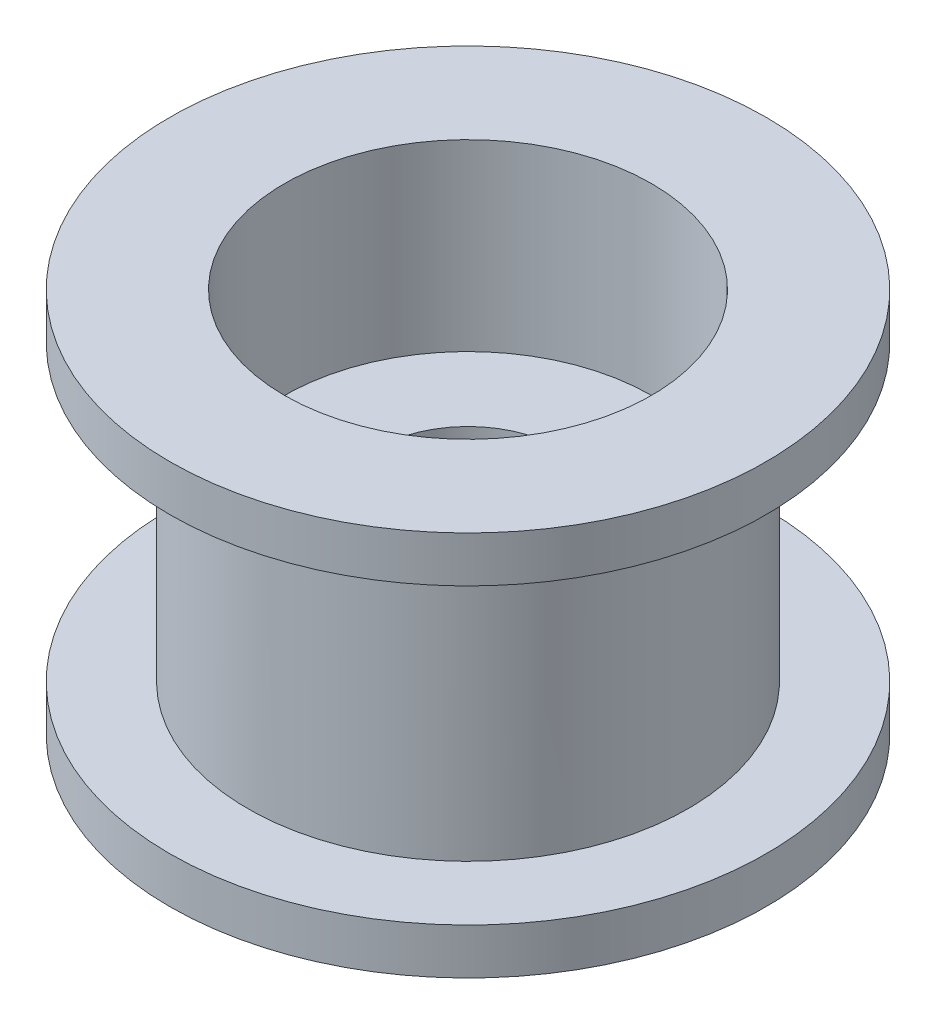
SolidWorks part; units mm, degrees
material "6061 Alloy"
ref_plane "Front Plane" through (0, 0, 0) normal (0, 0, 1) x (1, 0, 0)
ref_plane "Top Plane" through (0, 0, 0) normal (0, 1, 0) x (1, 0, 0)
ref_plane "Right Plane" through (0, 0, 0) normal (1, 0, 0) x (0, 0, -1)
sketch "BaseS" plane through (0, 0, 0) normal (0, 1, 0) x (1, 0, 0)
  circle A0 centre (0, 0) radius 4.8
  dimension "D1" = 9.6
extrude "Base" add sketch "BaseS" along normal mid plane 6.4
sketch "FlangeS" plane through (0, 3.2, 0) normal (0, 1, 0) x (1, 0, 0)
  circle A0 centre (0, 0) radius 6.5
  dimension "D1" = 13
extrude "Flange" add sketch "FlangeS" along normal blind 1
sketch "TopBoreS" plane through (0, 4.2, 0) normal (0, 1, 0) x (1, 0, 0)
  circle A0 centre (0, 0) radius 4
  dimension "D1" = 8
extrude "TopBore" cut sketch "TopBoreS" against normal blind 4
mirror "BoreVM" about plane through (0, 0, 0) normal (0, 1, 0) of "TopBore", "Flange"
sketch "ThruHoleS" plane through (0, 0.2, 0) normal (0, 1, 0) x (1, 0, 0)
  circle A0 centre (0, 0) radius 2
  dimension "D1" = 4
extrude "ThruHole" cut sketch "ThruHoleS" against normal through all
